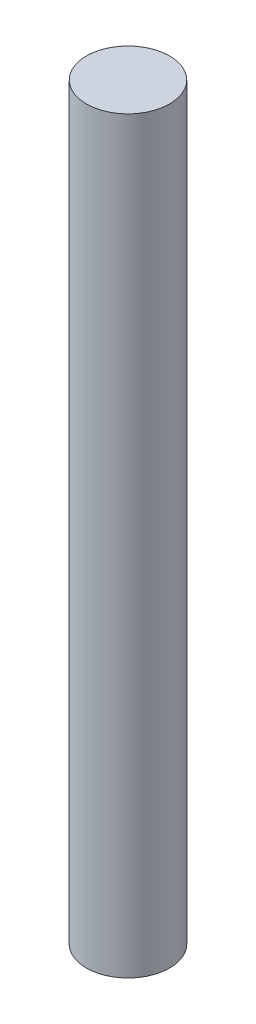
SolidWorks part; units mm, degrees
ref_plane "Ebene vorne" through (0, 0, 0) normal (0, 0, 1) x (1, 0, 0)
ref_plane "Ebene oben" through (0, 0, 0) normal (0, 1, 0) x (1, 0, 0)
ref_plane "Ebene rechts" through (0, 0, 0) normal (1, 0, 0) x (0, 0, -1)
sketch "Skizze1" plane through (0, 0, 0) normal (0, 1, 0) x (1, 0, 0)
  circle A0 centre (0, 0) radius 1
extrude "Aufsatz-Linear austragen1" add sketch "Skizze1" along normal blind 18
